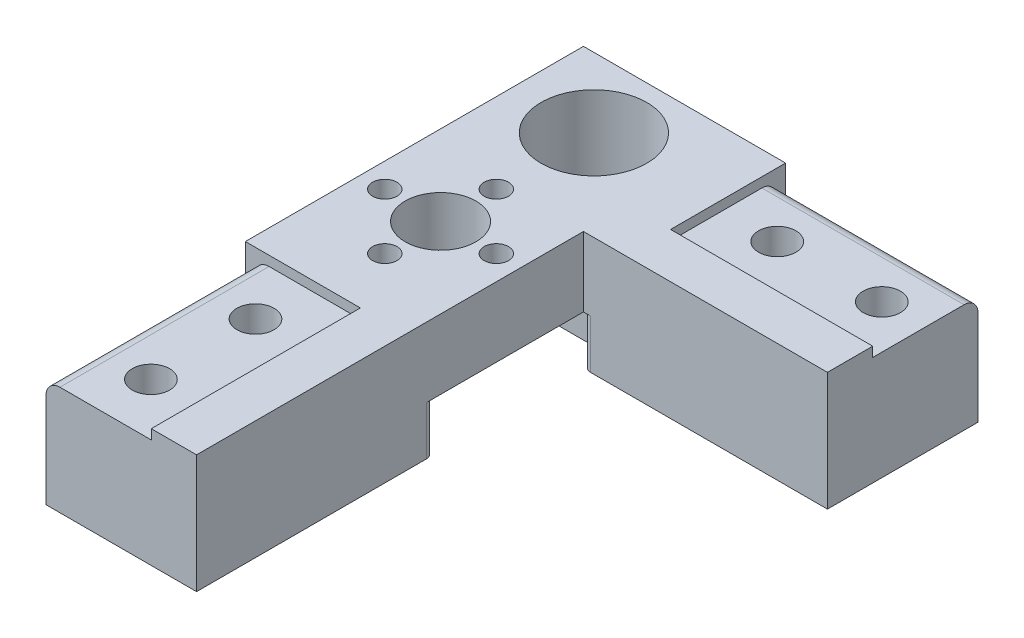
SolidWorks part; units mm, degrees
ref_plane "Alzado" through (0, 0, 0) normal (0, 0, 1) x (1, 0, 0)
ref_plane "Planta" through (0, 0, 0) normal (0, 1, 0) x (1, 0, 0)
ref_plane "Vista lateral" through (0, 0, 0) normal (1, 0, 0) x (0, 0, -1)
sketch "Croquis1" plane through (0, 0, 0) normal (0, 1, 0) x (1, 0, 0)
  line L0 (23, -63.5) -> (23, -23)
  line L1 (0, -63.5) -> (23, -63.5)
  line L2 (23, -23) -> (43, -23)
  line L8 (43, -23) -> (43, 0)
  line L10 (0, -63.5) -> (0, 0)
  line L11 (0, 0) -> (43, 0)
  dimension "D1" = 63.5
  dimension "D2" = 43
  dimension "D3" = 23
extrude "Saliente-Extruir2" add sketch "Croquis1" against normal blind 17
sketch "Croquis4" plane through (0, 0, 0) normal (0, -1, 0) x (-1, 0, 0)
  line L0 (-11.5, -10) -> (-11.5, -63.5) construction
  line L2 (0, -63.5) -> (-23, -63.5) construction
  line L4 (0, 0) -> (-43, 0) construction
  circle A6 centre (-11.5, -10) radius 7.575
  dimension "D1" = 10
  dimension "D3" = 15.15
extrude "Cortar-Extruir7" cut sketch "Croquis4" along normal through all
sketch "Croquis12" plane through (0, 0, 0) normal (0, 1, 0) x (1, 0, 0)
  line L0 (0, 0) -> (43, 0) construction
  circle A1 centre (11.5, -32) radius 5.075
  dimension "D3" = 10.15
  dimension "D1" = 32
extrude "Cortar-Extruir12" cut sketch "Croquis12" against normal through all
sketch "Croquis17" plane through (0, 0, 0) normal (0, 1, 0) x (1, 0, 0)
  circle A0 centre (11.5, -24) radius 1.75
  circle A1 centre (11.5, -40) radius 1.75
  circle A2 centre (3.5, -32) radius 1.75
  circle A3 centre (19.5, -32) radius 1.75
  circle A4 centre (11.5, -32) radius 8 construction
  dimension "D1" = 3.5
  dimension "D2" = 16
extrude "Cortar-Extruir15" cut sketch "Croquis17" against normal through all
sketch "Croquis8" plane through (43, 0, 0) normal (1, 0, 0) x (0, 0, -1)
  line L0 (0, -17) -> (0, 0)
  line L1 (0, 0) -> (-16.5, 0)
  line L2 (0, 0) -> (-23, 0) construction
  line L3 (-16.5, 0) -> (-16.5, -1.4)
  line L4 (-16.5, -1.4) -> (-1.4, -1.4)
  line L5 (-1.4, -1.4) -> (-1.4, -17)
  line L6 (-23, -17) -> (0, -17) construction
  line L7 (-1.4, -17) -> (0, -17)
  dimension "D1" = 1.4
  dimension "D2" = 16.5
extrude "Cortar-Extruir9" cut sketch "Croquis8" against normal blind 14
sketch "Croquis9" plane through (0, 0, 63.5) normal (0, 0, -1) x (-1, 0, 0)
  line L0 (0, -17) -> (-1.4, -17)
  line L1 (0, -17) -> (-23, -17) construction
  line L2 (-1.4, -17) -> (-1.4, -1.4)
  line L3 (-1.4, -1.4) -> (-16.5, -1.4)
  line L4 (-16.5, -1.4) -> (-16.5, 0)
  line L6 (-16.5, 0) -> (0, 0)
  line L8 (0, 0) -> (0, -17)
  dimension "D1" = 1.4
  dimension "D3" = 16.5
extrude "Cortar-Extruir10" cut sketch "Croquis9" along normal blind 15
sketch "Croquis10" plane through (0, -1.4, 0) normal (0, 1, 0) x (1, 0, 0)
  line L0 (29, -16.5) -> (29, -1.4) construction
  line L1 (16.5, -48.5) -> (16.5, -63.5) construction
  line L3 (43, -1.4) -> (43, -16.5) construction
  line L4 (43, -8.95) -> (36.75, -8.95) construction
  line L6 (8.95, -56) -> (1.4, -56) construction
  line L7 (1.4, -48.5) -> (1.4, -63.5) construction
  circle A0 centre (36.75, -8.95) radius 2.675
  circle A1 centre (8.95, -56) radius 2.675
  dimension "D1" = 5.35
  dimension "D3" = 7.55
  dimension "D2" = 7.75
extrude "Cortar-Extruir11" cut sketch "Croquis10" against normal blind 8.6
sketch "Croquis14" plane through (0, 0, 63.5) normal (0, 0, 1) x (1, 0, 0)
  line L8 (23, 0) -> (16.5, 0)
  line L9 (16.5, 0) -> (16.5, -1.4)
  line L10 (16.5, -1.4) -> (1.4, -1.4)
  line L11 (1.4, -1.4) -> (1.4, -17)
  line L14 (1.4, -17) -> (23, -17)
  line L15 (23, -17) -> (23, 0)
  line L16 (23, 0) -> (16.5, 0)
  line L17 (16.5, 0) -> (16.5, -1.4)
  line L18 (16.5, -1.4) -> (1.4, -1.4)
  line L19 (1.4, -1.4) -> (1.4, -17)
  line L22 (1.4, -17) -> (23, -17)
  line L23 (23, -17) -> (23, 0)
  dimension "D1" = 0
extrude "Saliente-Extruir3" add sketch "Croquis14" along normal blind 15
sketch "Croquis15" plane through (43, 0, 0) normal (1, 0, 0) x (0, 0, -1)
  line L9 (-1.4, -17) -> (-1.4, -1.4)
  line L10 (-1.4, -1.4) -> (-16.5, -1.4)
  line L11 (-16.5, -1.4) -> (-16.5, 0)
  line L12 (-16.5, 0) -> (-23, 0)
  line L13 (-23, 0) -> (-23, -17)
  line L14 (-23, -17) -> (-1.4, -17)
  line L17 (-1.4, -17) -> (-1.4, -1.4)
  line L18 (-1.4, -1.4) -> (-16.5, -1.4)
  line L19 (-16.5, -1.4) -> (-16.5, 0)
  line L20 (-16.5, 0) -> (-23, 0)
  line L21 (-23, 0) -> (-23, -17)
  line L22 (-23, -17) -> (-1.4, -17)
  dimension "D1" = 0
extrude "Saliente-Extruir4" add sketch "Croquis15" along normal blind 15
sketch "Croquis16" plane through (0, -1.4, 0) normal (0, 1, 0) x (1, 0, 0)
  line L0 (8.95, -71) -> (8.95, -56) construction
  line L2 (51.75, -8.95) -> (36.75, -8.95) construction
  circle A0 centre (8.95, -71) radius 2.675
  circle A1 centre (51.75, -8.95) radius 2.675
  circle A2 centre (8.95, -56) radius 2.675 construction
  circle A3 centre (36.75, -8.95) radius 2.675 construction
  dimension "D1" = 15
extrude "Cortar-Extruir14" cut sketch "Croquis16" against normal blind 8.6
sketch "Croquis18" plane through (0, -17, 0) normal (0, -1, 0) x (1, 0, 0)
  line L0 (0, 19.5) -> (23, 19.5)
  line L1 (23, 44.5) -> (23, 19.5)
  line L2 (23, 78.5) -> (23, 23) construction
  line L4 (0, 44.5) -> (23, 19.5) construction
  line L5 (1.4, 78.5) -> (23, 78.5) construction
  line L6 (23, 23) -> (23, 78.5)
  line L7 (23, 78.5) -> (1.4, 78.5)
  line L8 (0, 48.5) -> (0, 0)
  line L9 (0, 0) -> (29, 0)
  line L10 (58, 1.4) -> (58, 23)
  line L11 (58, 23) -> (23, 23)
  line L13 (23, 44.5) -> (0, 44.5)
  line L14 (0, 44.5) -> (0, 19.5)
  line L21 (1.4, 78.5) -> (1.4, 48.5)
  line L23 (1.4, 48.5) -> (0, 48.5)
  line L26 (29, 0) -> (29, 1.4)
  line L28 (29, 1.4) -> (58, 1.4)
  circle A0 centre (11.5, 32) radius 5.075 construction
  dimension "D2" = 34
  dimension "D1" = 0
extrude "Cortar-Extruir16" cut sketch "Croquis18" against normal blind 7
sketch "Croquis19" plane through (0, -10, 0) normal (0, -1, 0) x (1, 0, 0)
  line L1 (14.6754, 40) -> (13.0877, 42.75)
  line L2 (13.0877, 42.75) -> (9.9123, 42.75)
  line L3 (9.9123, 42.75) -> (8.3246, 40)
  line L4 (8.3246, 40) -> (9.9123, 37.25)
  line L5 (9.9123, 37.25) -> (13.0877, 37.25)
  line L6 (13.0877, 37.25) -> (14.6754, 40)
  line L7 (22.25, 30.4123) -> (22.25, 33.5877)
  line L8 (22.25, 33.5877) -> (19.5, 35.1754)
  line L9 (19.5, 35.1754) -> (16.75, 33.5877)
  line L10 (16.75, 33.5877) -> (16.75, 30.4123)
  line L11 (16.75, 30.4123) -> (19.5, 28.8246)
  line L12 (19.5, 28.8246) -> (22.25, 30.4123)
  line L13 (14.6754, 24) -> (13.0877, 26.75)
  line L14 (13.0877, 26.75) -> (9.9123, 26.75)
  line L15 (9.9123, 26.75) -> (8.3246, 24)
  line L16 (8.3246, 24) -> (9.9123, 21.25)
  line L17 (9.9123, 21.25) -> (13.0877, 21.25)
  line L18 (13.0877, 21.25) -> (14.6754, 24)
  line L19 (0.75, 33.5877) -> (0.75, 30.4123)
  line L20 (0.75, 30.4123) -> (3.5, 28.8246)
  line L21 (3.5, 28.8246) -> (6.25, 30.4123)
  line L22 (6.25, 30.4123) -> (6.25, 33.5877)
  line L23 (6.25, 33.5877) -> (3.5, 35.1754)
  line L24 (3.5, 35.1754) -> (0.75, 33.5877)
  circle A0 centre (11.5, 40) radius 2.75 construction
  circle A1 centre (19.5, 32) radius 2.75 construction
  circle A2 centre (11.5, 24) radius 2.75 construction
  circle A3 centre (3.5, 32) radius 2.75 construction
  dimension "D1" = 5.5
extrude "Cortar-Extruir17" cut sketch "Croquis19" against normal blind 2.5
fillet "Redondeo2" radius 1 5 edges at (0, -13.5, 19.5) (23, -13.5, 23) (23, -13.5, 19.5) (23, -13.5, 44.5) (0, -13.5, 44.5)
fillet "Redondeo4" radius 2 2 edges at (43.5, -1.4, 1.4) (1.4, -1.4, 63.5)
